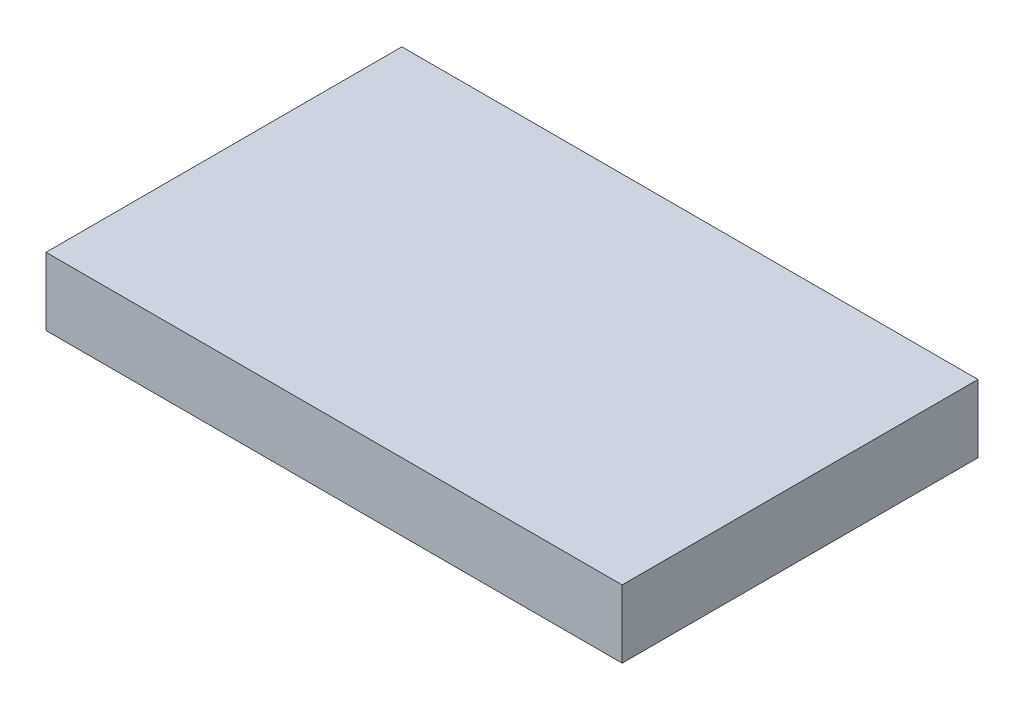
SolidWorks part; units mm, degrees
ref_plane "Front Plane" through (0, 0, 0) normal (0, 0, 1) x (1, 0, 0)
ref_plane "Top Plane" through (0, 0, 0) normal (0, 1, 0) x (1, 0, 0)
ref_plane "Right Plane" through (0, 0, 0) normal (1, 0, 0) x (0, 0, -1)
sketch "Sketch1" plane through (0, 0, 0) normal (0, 1, 0) x (1, 0, 0)
  line L1 (-8.5, 5.25) -> (8.5, 5.25)
  line L2 (-8.5, 5.25) -> (-8.5, -5.25)
  line L3 (-8.5, -5.25) -> (8.5, -5.25)
  line L4 (8.5, 5.25) -> (8.5, -5.25)
  line L5 (-8.5, 5.25) -> (8.5, -5.25) construction
  line L6 (-8.5, -5.25) -> (8.5, 5.25) construction
  point P0 (0, 0)
  dimension "D1" = 10.5
  dimension "D2" = 17
extrude "Boss-Extrude1" add sketch "Sketch1" along normal blind 2
